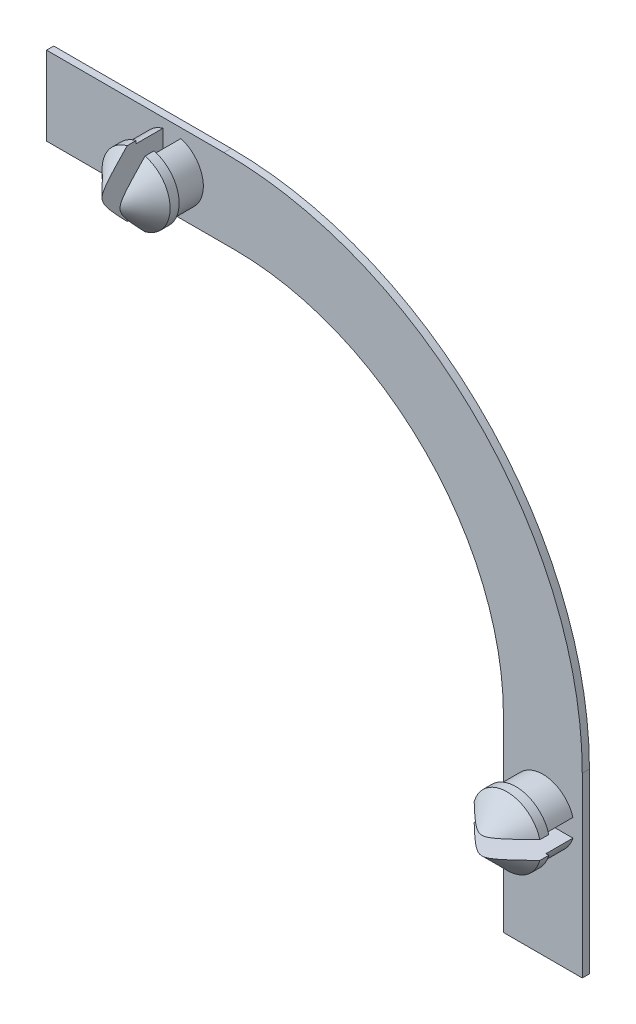
SolidWorks part; units mm, degrees
ref_plane "Přední rovina" through (0, 0, 0) normal (0, 0, 1) x (1, 0, 0)
ref_plane "Horní rovina" through (0, 0, 0) normal (0, 1, 0) x (1, 0, 0)
ref_plane "Pravá rovina" through (0, 0, 0) normal (1, 0, 0) x (0, 0, -1)
sketch "Skica1" plane through (0, 0, 0) normal (0, 0, 1) x (1, 0, 0)
  line L1 (-22.0167, 8.8677) -> (7.8833, 8.8677)
  line L2 (-22.0167, 8.8677) -> (-22.0167, 4.4677)
  line L3 (-22.0167, 4.4677) -> (7.8833, 4.4677)
  line L4 (7.8833, 8.8677) -> (7.8833, 4.4677)
  line L5 (7.8833, 4.4677) -> (3.4833, 4.4677)
  line L6 (7.8833, 4.4677) -> (7.8833, -21.0323)
  line L7 (7.8833, -21.0323) -> (3.4833, -21.0323)
  line L8 (3.4833, 4.4677) -> (3.4833, -21.0323)
  dimension "D1" = 4.4
  dimension "D2" = 29.9
  dimension "D3" = 25.5
  dimension "D4" = 4.4
extrude "Přidat vysunutím1" add sketch "Skica1" along normal blind 0.4 contours L4 L1 L2 L3 | L3 L8 L7 L6
fillet "Zaoblit3" radius 15 1 edges at (3.4833, 4.4677, 0.2)
fillet "Zaoblit4" radius 20 1 edges at (7.8833, 8.8677, 0.2)
sketch "Skica2" plane through (0, 0, 0.4) normal (0, 0, 1) x (1, 0, 0)
  line L0 (-22.0167, 8.8677) -> (-22.0167, 4.4677) construction
  line L1 (-22.0167, 4.4677) -> (-11.5167, 4.4677) construction
  line L2 (7.8833, -21.0323) -> (3.4833, -21.0323) construction
  line L3 (3.4833, -10.5323) -> (3.4833, -21.0323) construction
  circle A0 centre (-15.0167, 6.6677) radius 1.75
  circle A1 centre (5.6833, -14.0323) radius 1.75
  point P8 (-15.2917, 5.7631)
  dimension "D1" = 3.5
  dimension "D2" = 3.5
  dimension "D3" = 7
  dimension "D4" = 2.2
  dimension "D5" = 7
  dimension "D6" = 2.2
extrude "Přidat vysunutím2" add sketch "Skica2" along normal blind 1.5
sketch "Skica3" plane through (0, 0, 1.9) normal (0, 0, 1) x (1, 0, 0)
  circle A1 centre (-15.0167, 6.6677) radius 1.9
  circle A2 centre (5.6833, -14.0323) radius 1.9
  circle A3 centre (5.6833, -14.0323) radius 1.75 construction
  dimension "D1" = 3.8
  dimension "D2" = 3.8
extrude "Přidat vysunutím3" add sketch "Skica3" along normal blind 2
chamfer "Zkosení1" distance 1.5 angle 45 2 edges at (7.5833, -14.0323, 3.9) (-13.1167, 6.6677, 3.9)
sketch "Skica4" plane through (0, 0, 3.9) normal (0, 0, 1) x (1, 0, 0)
  line L1 (3.7833, -13.5323) -> (7.5833, -13.5323)
  line L2 (3.7833, -13.5323) -> (3.7833, -14.5323)
  line L3 (3.7833, -14.5323) -> (7.5833, -14.5323)
  line L4 (7.5833, -13.5323) -> (7.5833, -14.5323)
  line L5 (3.7833, -13.5323) -> (7.5833, -14.5323) construction
  line L6 (3.7833, -14.5323) -> (7.5833, -13.5323) construction
  line L7 (-15.5167, 8.5677) -> (-14.5167, 8.5677)
  line L8 (-15.5167, 8.5677) -> (-15.5167, 4.7677)
  line L9 (-15.5167, 4.7677) -> (-14.5167, 4.7677)
  line L10 (-14.5167, 8.5677) -> (-14.5167, 4.7677)
  line L11 (-15.5167, 8.5677) -> (-14.5167, 4.7677) construction
  line L12 (-15.5167, 4.7677) -> (-14.5167, 8.5677) construction
  point P0 (5.6833, -14.0323)
  point P5 (-15.0167, 6.6677)
  dimension "D1" = 1
  dimension "D2" = 3.8
  dimension "D3" = 3.8
  dimension "D4" = 1
extrude "Odebrat vysunutím1" cut sketch "Skica4" against normal blind 3.5
